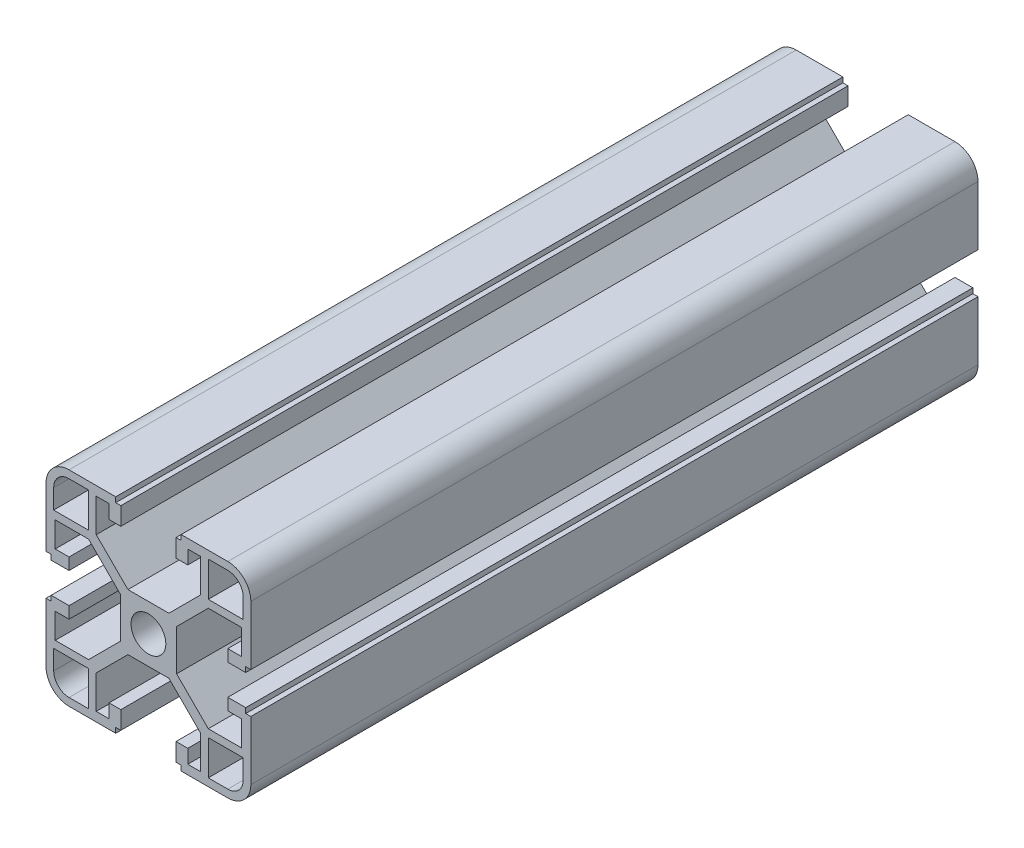
SolidWorks part; units mm, degrees
material "6061-T6 (SS)"
ref_plane "Front Plane" through (0, 0, 0) normal (0, 0, 1) x (1, 0, 0)
ref_plane "Top Plane" through (0, 0, 0) normal (0, 1, 0) x (1, 0, 0)
ref_plane "Right Plane" through (0, 0, 0) normal (1, 0, 0) x (0, 0, -1)
sketch "Sketch1" plane through (0, 0, 0) normal (0, 0, 1) x (1, 0, 0)
  line L0 (3.4, 0) -> (5.5, 0)
  line L1 (10.19, 11.69) -> (4, 5.5)
  line L2 (11.69, 10.19) -> (5.5, 4)
  line L3 (18.2, 10.19) -> (11.69, 10.19)
  line L4 (18.2, 10.19) -> (18.2, 5.2656)
  line L5 (18.2, 5.2656) -> (15.5, 5.2656)
  line L6 (15.5, 5.2656) -> (15.5, 2.9656)
  line L7 (15.5, 2.9656) -> (19, 2.9656)
  line L8 (19, 2.9656) -> (19, 3.9656)
  line L9 (19, 3.9656) -> (20, 3.9656)
  line L10 (20, 3.9656) -> (20, 15.5)
  line L11 (15.5, 20) -> (6.3853, 20)
  line L12 (18.5, 11.69) -> (18.5, 15.5)
  line L13 (15.5, 18.5) -> (11.69, 18.5)
  line L14 (11.69, 11.69) -> (11.69, 18.5)
  line L15 (0, 3.4) -> (0, 5.5)
  line L16 (4, 5.5) -> (0, 5.5)
  line L17 (6.3853, 20) -> (6.3853, 19)
  line L18 (5.5, 0) -> (5.5, 4)
  line L19 (6.3853, 19) -> (5.3853, 19)
  line L20 (5.3853, 19) -> (5.3853, 15.5)
  line L21 (5.3853, 15.5) -> (7.6853, 15.5)
  line L22 (10.19, 11.69) -> (10.19, 18.2)
  line L23 (11.69, 11.69) -> (18.5, 11.69)
  line L24 (7.6853, 18.2) -> (7.6853, 15.5)
  line L25 (10.19, 18.2) -> (7.6853, 18.2)
  arc A0 (20, 15.5) -> (15.5, 20) centre (15.5, 15.5) ccw
  arc A1 (18.5, 15.5) -> (15.5, 18.5) centre (15.5, 15.5) ccw
  arc A2 (3.4, 0) -> (0, 3.4) centre (0, 0) ccw
  dimension "D3" = 4.5
  dimension "D18" = 1.5
  dimension "D9" = 3.4
  dimension "D20" = 1.8
  dimension "D25" = 3
  dimension "D1" = 5.5
  dimension "D2" = 1.5
  dimension "D4" = 14.5
  dimension "D5" = 1.5
  dimension "D6" = 2.1
  dimension "D7" = 2.3
  dimension "D8" = 1.8
  dimension "D10" = 6.81
  dimension "D11" = 2.1
  dimension "D12" = 1
  dimension "D13" = 4.5
  dimension "D14" = 45
  dimension "D15" = 14.5
  dimension "D16" = 1
  dimension "D17" = 1.5
  dimension "D19" = 6.81
  dimension "D21" = 4.5
  dimension "D22" = 2.3
  dimension "D23" = 1
  dimension "D24" = 1
  dimension "D26" = 8.754
  dimension "D27" = 8.754
  dimension "D28" = 4.9244
  dimension "D29" = 2.5047
extrude "Boss-Extrude1" add sketch "Sketch1" along normal blind 142
mirror "Mirror1" about plane through (0, 0, 0) normal (0, 1, 0) of "Boss-Extrude1"
mirror "Mirror2" about plane through (0, 0, 0) normal (1, 0, 0) of "Boss-Extrude1"
mirror "Mirror3" about plane through (0, 0, 0) normal (0, 1, 0) of "Mirror2"
